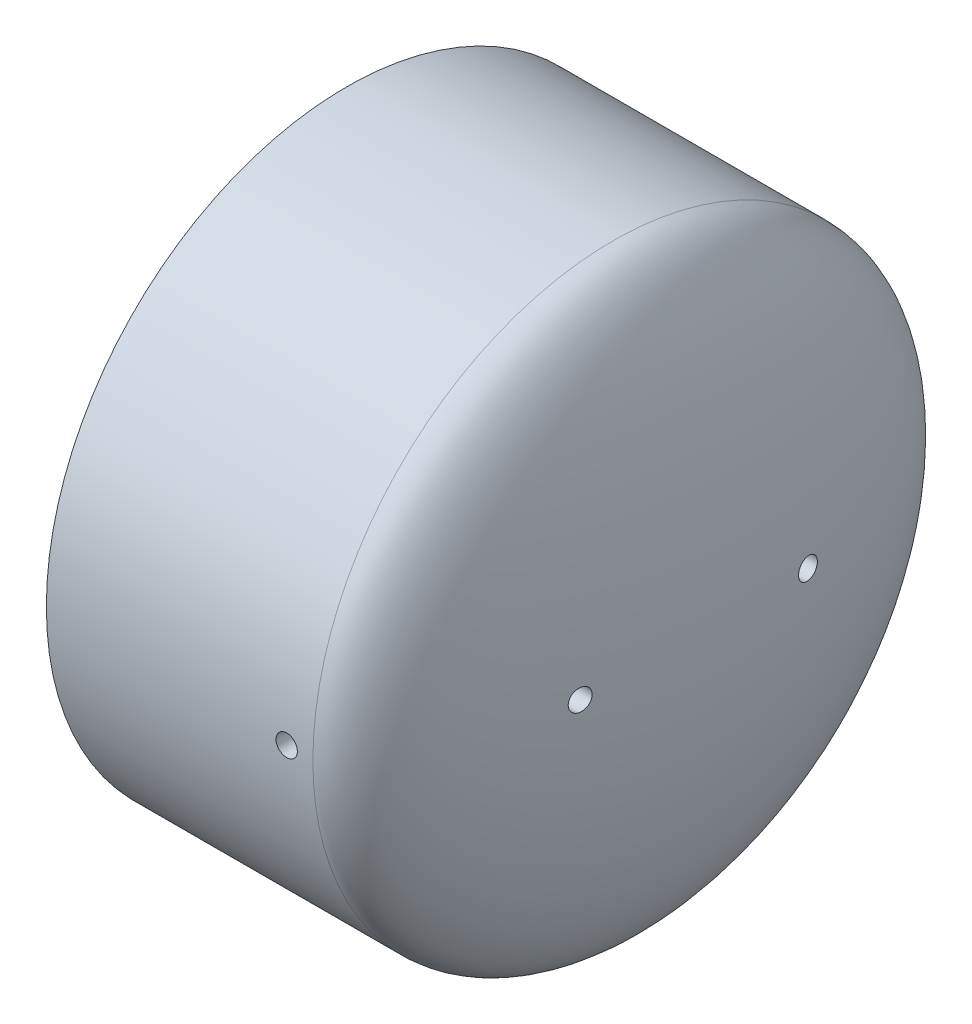
SolidWorks part; units mm, degrees
ref_plane "Front Plane" through (0, 0, 0) normal (0, 0, 1) x (1, 0, 0)
ref_plane "Top Plane" through (0, 0, 0) normal (0, 1, 0) x (1, 0, 0)
ref_plane "Right Plane" through (0, 0, 0) normal (1, 0, 0) x (0, 0, -1)
sketch "Sketch0" plane through (0, 0, 0) normal (0, 0, 1) x (1, 0, 0)
  line L0 (-78.994, 0) -> (0, 0) construction
  line L2 (-19.558, 0) -> (0, 0) construction
  line L4 (-78.994, 66.929) -> (-78.994, -66.929) construction
  line L5 (-19.558, 57.0357) -> (-78.994, 57.3786) construction
  line L6 (-19.558, 57.0357) -> (-19.558, -57.0357) construction
  line L7 (-19.558, -57.0357) -> (-78.994, -57.3786) construction
  line L8 (-78.994, 57.3786) -> (-78.994, -57.3786) construction
  line L14 (-19.558, 48.5902) -> (-19.558, -48.5902) construction
  dimension "M" = 133.858
  dimension "OD A" = 114.7572
  dimension "OD B" = 114.0714
  dimension "ID" = 97.1804
  dimension "W" = 78.994
  dimension "C" = 59.436
sketch "Sketch1" plane through (0, 0, 0) normal (0, 0, 1) x (1, 0, 0)
  line L0 (-78.994, 0) -> (0, 0) construction
  line L1 (-78.994, 0) -> (0, 0) construction
  line L2 (-19.558, 0) -> (0, 0) construction
  line L3 (-78.994, -66.929) -> (-19.558, -66.929)
  line L4 (-78.994, -66.929) -> (-78.994, -57.3786)
  line L5 (-78.994, -57.3786) -> (-19.558, -57.0357)
  line L6 (-19.558, 0) -> (-19.558, -57.0357) construction
  line L7 (-19.558, -57.0357) -> (-19.558, -66.929) construction
  line L8 (-9.8933, 0) -> (0, 0)
  ellipse E0 centre (-19.558, 0) end of major axis (-19.558, 66.929) minor radius 19.558 (-19.558, -66.929) -> (0, 0) ccw
  ellipse E1 centre (-19.558, 0) end of major axis (-19.558, -57.0357) minor radius 9.6647 (-19.558, -57.0357) -> (-9.8933, 0) ccw
revolve "Revolve1" add sketch "Sketch1" angle 360 about L1
sketch "Sketch2" plane through (0, 0, 0) normal (1, 0, 0) x (0, 0, -1)
  circle A0 centre (-25.4, 0) radius 2.3813
  circle A1 centre (25.4, 0) radius 2.3812
  dimension "D1" = 4.7625
  dimension "D2" = 4.7625
  dimension "D3" = 25.4
  dimension "D4" = 25.4
extrude "Cut-Extrude3" cut sketch "Sketch2" against normal through all
sketch "Sketch3" plane through (0, 0, 0) normal (0, 0, 1) x (1, 0, 0)
  circle A0 centre (-25.4, 0) radius 2.3812
  dimension "D1" = 4.7625
  dimension "D2" = 25.4
extrude "Cut-Extrude4" cut sketch "Sketch3" against normal through all both and the other way through all
